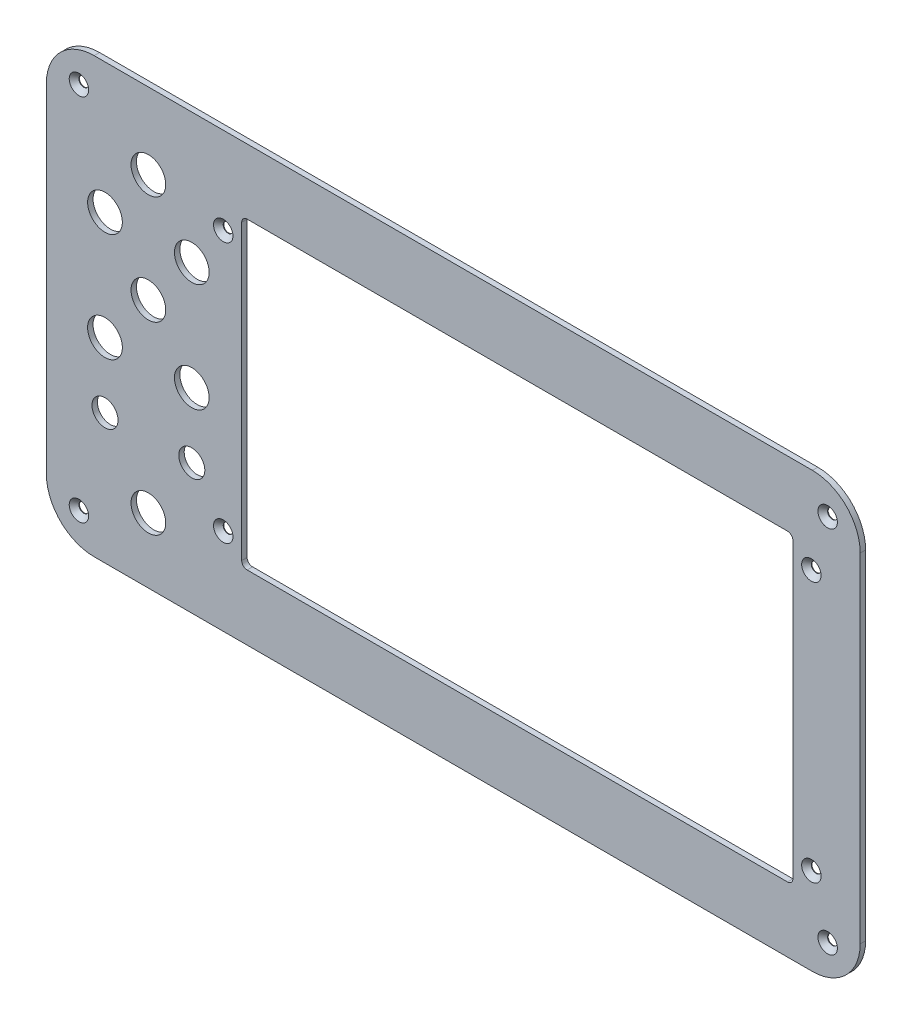
SolidWorks part; units mm, degrees
material "7079 Alloy"
ref_plane "Front" through (0, 0, 0) normal (0, 0, 1) x (1, 0, 0)
ref_plane "Top" through (0, 0, 0) normal (0, 1, 0) x (1, 0, 0)
ref_plane "Right" through (0, 0, 0) normal (1, 0, 0) x (0, 0, -1)
sketch "Sketch1" plane through (0, 0, 0) normal (0, 0, 1) x (1, 0, 0)
  line L0 (187.5, -100) -> (-187.5, 100) construction
  line L1 (-165.5, 100) -> (165.5, 100)
  line L2 (-187.5, 78) -> (-187.5, -78)
  line L3 (-165.5, -100) -> (165.5, -100)
  line L4 (187.5, 78) -> (187.5, -78)
  arc A0 (187.5, -78) -> (165.5, -100) centre (165.5, -78) cw
  arc A1 (165.5, 100) -> (187.5, 78) centre (165.5, 78) cw
  arc A2 (-187.5, 78) -> (-165.5, 100) centre (-165.5, 78) cw
  arc A3 (-165.5, -100) -> (-187.5, -78) centre (-165.5, -78) cw
  point P10 (187.5, 100)
  point P16 (-187.5, -100)
  dimension "D3" = 22
  dimension "D1" = 375
  dimension "D2" = 200
extrude "Extrude1" add sketch "Sketch1" along normal mid plane 2.5
sketch "Sketch5" plane through (0, 0, 1.25) normal (0, 0, 1) x (1, 0, 0)
  line L0 (156.5, -70) -> (-97.5, 70) construction
  line L1 (-95, 70) -> (154, 70)
  line L2 (-97.5, 67.5) -> (-97.5, -67.5)
  line L3 (-95, -70) -> (154, -70)
  line L4 (156.5, 67.5) -> (156.5, -67.5)
  line L5 (165.5, 100) -> (-165.5, 100) construction
  line L8 (-187.5, 78) -> (-187.5, -78) construction
  line L9 (187.5, -78) -> (187.5, 78) construction
  line L10 (-165.5, -100) -> (165.5, -100) construction
  arc A0 (156.5, 67.5) -> (154, 70) centre (154, 67.5) ccw
  arc A1 (156.5, -67.5) -> (154, -70) centre (154, -67.5) cw
  arc A2 (-95, -70) -> (-97.5, -67.5) centre (-95, -67.5) cw
  arc A3 (-97.5, 67.5) -> (-95, 70) centre (-95, 67.5) cw
  dimension "D3" = 2.5
  dimension "D1" = 30
  dimension "D2" = 90
  dimension "D4" = 31
  dimension "D5" = 30
extrude "Cut-Extrude4" cut sketch "Sketch5" against normal through all
hole_wizard "Escareado para parafuso Allen sextavado escareado de M41" positions "Esboço2" profile "Esboço1" countersink size "M4" standard "ISO" end condition through all
sketch "Esboço2" plane through (0, 0, 1.25) normal (0, 0, 1) x (1, 0, 0)
  line L0 (187.5, -78) -> (187.5, 78) construction
  line L1 (165.5, 100) -> (-165.5, 100) construction
  point P0 (172.5, 85)
  dimension "D1" = 15
  dimension "D2" = 15
sketch "Esboço1" plane through (172.5, 85, 1.25) normal (1, 0, 0) x (0, -1, 0)
  line L0 (0, 0) -> (0, 2.5)
  line L1 (0, 2.5) -> (2.25, 2.5)
  line L2 (2.25, 2.5) -> (2.25, 2.23)
  line L3 (2.25, 2.23) -> (4.48, 0)
  line L5 (4.48, 0) -> (0, 0)
  line L6 (-2.25, 2.23) -> (-4.48, 0) construction
  line L11 (0, -6.35) -> (0, 107.95) construction
  dimension "Thru Hole Dia." = 4.5
  dimension "Thru Hole Depth" = 2.5
  dimension "Near C'Sink Dia." = 8.96
  dimension "Near C'Sink Angle" = 90
mirror "Espelhar2" about plane through (0, 0, 0) normal (1, 0, 0) of "Escareado para parafuso Allen sextavado escareado de M41"
mirror "Espelhar3" about plane through (0, 0, 0) normal (0, 1, 0) of "Escareado para parafuso Allen sextavado escareado de M41", "Espelhar2"
sketch "Esboço6" plane through (0, 0, 1.25) normal (0, 0, 1) x (1, 0, 0)
  line L0 (-165.5, -100) -> (165.5, -100) construction
  line L1 (-97.5, 67.5) -> (-97.5, -67.5) construction
  line L2 (-95, -70) -> (154, -70) construction
  line L3 (-140.5, 80.5381) -> (-140.5, -98.8543) construction
  line L4 (154, 70) -> (-95, 70) construction
  circle A9 centre (-140.5, 65) radius 8
  circle A10 centre (-120.5, 40) radius 8
  circle A11 centre (-160.5, 40) radius 8
  circle A12 centre (-140.5, 15) radius 8
  circle A13 centre (-120.5, -10) radius 8
  circle A14 centre (-160.5, -10) radius 8
  circle A15 centre (-140.5, -70) radius 8
  circle A16 centre (-120.5, -40) radius 6
  circle A17 centre (-160.5, -40) radius 6
  dimension "D1" = 30
  dimension "D2" = 43
  dimension "D4" = 30
  dimension "D5" = 25
  dimension "D6" = 25
  dimension "D7" = 25
  dimension "D8" = 30
  dimension "D9" = 30
  dimension "D10" = 5
  dimension "D13" = 20
  dimension "D14" = 20
extrude "Corte-extrusão1" cut sketch "Esboço6" against normal blind 10
sketch "Esboço7" plane through (0, 0, 1.25) normal (0, 0, 1) x (1, 0, 0)
  line L0 (-97.5, 67.5) -> (-97.5, -67.5) construction
  line L3 (-95, -70) -> (154, -70) construction
  line L6 (154, 70) -> (-95, 70) construction
  line L7 (156.5, -67.5) -> (156.5, 67.5) construction
  circle A0 centre (-106, -60) radius 1
  circle A1 centre (-106, 60) radius 1
  circle A2 centre (165, 60) radius 1
  circle A3 centre (165, -60) radius 1
  circle A4 centre (172.5, -85) radius 4.48 construction
  circle A5 centre (172.5, 85) radius 4.48 construction
  circle A6 centre (172.5, 85) radius 2.25 construction
  dimension "D1" = 8.5
  dimension "D3" = 8.5
  dimension "D6" = 25
  dimension "D7" = 25
  dimension "D8" = 7.5
  dimension "D9" = 7.5
  dimension "D2" = 10
  dimension "D4" = 120
  dimension "D5" = 10
extrude "Corte-extrusão2" cut sketch "Esboço7" against normal through all
hole_wizard "Escareado para parafuso Allen sextavado escareado de M42" positions "3DSketch4" profile "Esboço11" countersink size "M4" standard "ISO" end condition through all
sketch3d "3DSketch4"
  line L0 (-106, 60, -1.25) -> (-106, 60, 1.25) construction
  line L1 (-106, -60, -1.25) -> (-106, -60, 1.25) construction
  line L2 (165, -60, -1.25) -> (165, -60, 1.25) construction
  line L3 (165, 60, -1.25) -> (165, 60, 1.25) construction
  point P0 (-106, 60, 1.25)
  point P4 (-106, -60, 1.25)
  point P8 (165, -60, 1.25)
  point P12 (165, 60, 1.25)
sketch "Esboço11" plane through (-106, 60, 1.25) normal (1, 0, 0) x (0, -1, 0)
  line L0 (0, 0) -> (0, 2.5)
  line L1 (0, 2.5) -> (2.25, 2.5)
  line L2 (2.25, 2.5) -> (2.25, 2.23)
  line L3 (2.25, 2.23) -> (4.48, 0)
  line L5 (4.48, 0) -> (0, 0)
  line L6 (-2.25, 2.23) -> (-4.48, 0) construction
  line L11 (0, -6.35) -> (0, 107.95) construction
  dimension "Thru Hole Dia." = 4.5
  dimension "Thru Hole Depth" = 2.5
  dimension "Near C'Sink Dia." = 8.96
  dimension "Near C'Sink Angle" = 90
